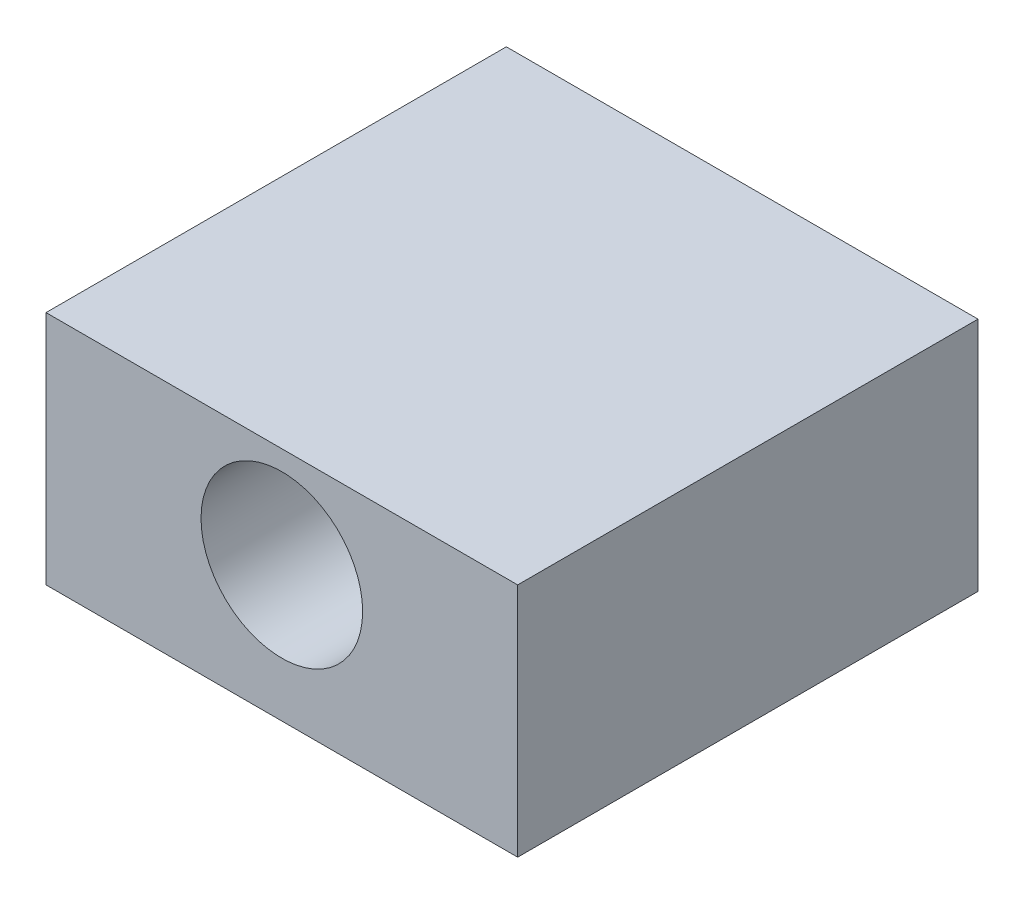
SolidWorks part; units mm, degrees
material "6061-T6 (SS)"
ref_plane "Front Plane" through (0, 0, 0) normal (0, 0, 1) x (1, 0, 0)
ref_plane "Top Plane" through (0, 0, 0) normal (0, 1, 0) x (1, 0, 0)
ref_plane "Right Plane" through (0, 0, 0) normal (1, 0, 0) x (0, 0, -1)
sketch "Sketch1" plane through (0, 0, 0) normal (0, 0, 1) x (1, 0, 0)
  line L1 (-9.525, -4.7625) -> (9.525, -4.7625)
  line L2 (-9.525, -4.7625) -> (-9.525, 4.7625)
  line L3 (-9.525, 4.7625) -> (9.525, 4.7625)
  line L4 (9.525, -4.7625) -> (9.525, 4.7625)
  line L5 (-9.525, -4.7625) -> (9.525, 4.7625) construction
  line L6 (-9.525, 4.7625) -> (9.525, -4.7625) construction
  point P0 (0, 0)
  dimension "D1" = 19.05
  dimension "D2" = 9.525
extrude "Extrude1" add sketch "Sketch1" along normal blind 18.5928
sketch "Sketch2" plane through (0, 0, 18.5928) normal (0, 0, 1) x (1, 0, 0)
  line L0 (0, 4.7625) -> (0, 0.6985) construction
  line L1 (9.525, 4.7625) -> (-9.525, 4.7625) construction
  dimension "D1" = 4.064
hole_wizard "1/4 Clearance Hole1" positions "3DSketch2" profile "Sketch4" hole size "1/4" standard "Ansi Inch"
sketch3d "3DSketch2"
  point P2 (0, 0.6985, 18.5928)
sketch "Sketch4" plane through (0, 0.6985, 18.5928) normal (1, 0, 0) x (0, -1, 0)
  line L0 (0, 0) -> (0, 17.2011)
  line L1 (0, 17.2011) -> (3.2639, 15.24)
  line L2 (3.2639, 15.24) -> (3.2639, 0)
  line L5 (3.2639, 0) -> (0, 0)
  line L10 (0, 17.2011) -> (-3.2639, 15.24) construction
  line L11 (0, -6.35) -> (0, 107.95) construction
  dimension "Hole Dia." = 6.5278
  dimension "Hole Depth" = 15.24
  dimension "Drill Angle" = 118
